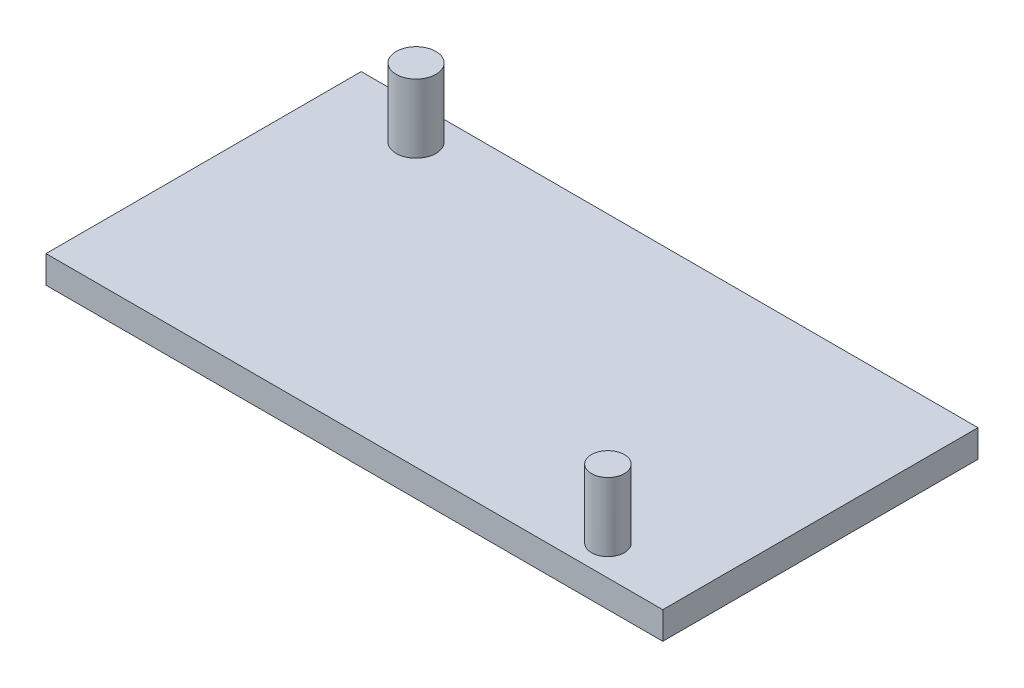
SolidWorks part; units mm, degrees
ref_plane "Front Plane" through (0, 0, 0) normal (0, 0, 1) x (1, 0, 0)
ref_plane "Top Plane" through (0, 0, 0) normal (0, 1, 0) x (1, 0, 0)
ref_plane "Right Plane" through (0, 0, 0) normal (1, 0, 0) x (0, 0, -1)
sketch "Sketch1" plane through (0, 0, 0) normal (0, 1, 0) x (1, 0, 0)
  line L1 (0, 0) -> (45, 0)
  line L2 (0, 0) -> (0, 23)
  line L3 (0, 23) -> (45, 23)
  line L4 (45, 0) -> (45, 23)
  dimension "D1" = 23
  dimension "D2" = 45
extrude "Boss-Extrude1" add sketch "Sketch1" against normal blind 2
sketch "Sketch2" plane through (0, 0, 0) normal (0, 1, 0) x (1, 0, 0)
  line L2 (0, 0) -> (45, 0) construction
  line L3 (45, 0) -> (45, 23) construction
  circle A0 centre (38.8, 2.2) radius 1.2
  dimension "D2" = 2.4
  dimension "D3" = 2.2
  dimension "D4" = 6.2
extrude "Boss-Extrude2" add sketch "Sketch2" along normal blind 5
sketch "Sketch3" plane through (0, 0, 0) normal (0, 1, 0) x (1, 0, 0)
  line L0 (45, 23) -> (0, 23) construction
  line L1 (0, 23) -> (0, 0) construction
  circle A0 centre (6.45, 20.55) radius 1.45
  dimension "D1" = 2.9
  dimension "D2" = 2.45
  dimension "D3" = 6.45
extrude "Boss-Extrude3" add sketch "Sketch3" along normal blind 5
